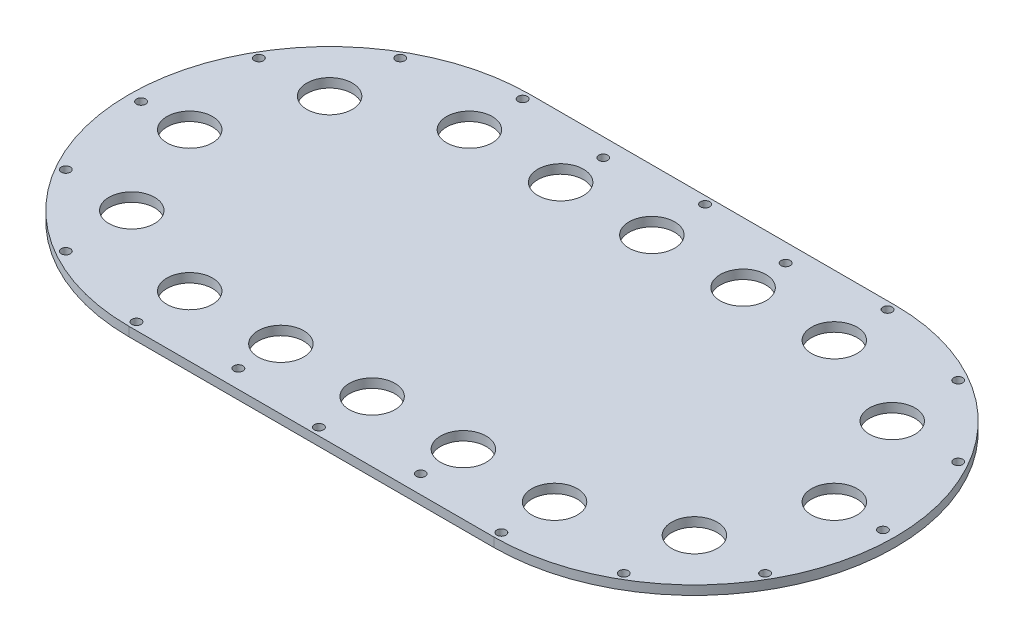
SolidWorks part; units mm, degrees
ref_plane "前视基准面" through (0, 0, 0) normal (0, 0, 1) x (1, 0, 0)
ref_plane "上视基准面" through (0, 0, 0) normal (0, 1, 0) x (1, 0, 0)
ref_plane "右视基准面" through (0, 0, 0) normal (1, 0, 0) x (0, 0, -1)
sketch "草图1" plane through (0, 0, 0) normal (0, 1, 0) x (1, 0, 0)
  line L0 (0, 0) -> (0, 89.0672) construction
  line L1 (-60, 0) -> (60, 0) construction
  line L2 (-60, 70) -> (60, 70)
  line L3 (-60, -70) -> (60, -70)
  line L4 (-90, 51.9615) -> (-60, 0) construction
  line L5 (-90, -51.9615) -> (-60, 0) construction
  line L8 (0, 0) -> (76.6344, 0) construction
  line L9 (-49.5811, 59.0885) -> (-60, 0) construction
  line L10 (-116.3816, -20.5212) -> (-60, 0) construction
  line L11 (-14.0373, -38.5673) -> (-60, 0) construction
  arc A2 (-60, 70) -> (-60, -70) centre (-60, 0) ccw
  arc A3 (60, -70) -> (60, 70) centre (60, 0) ccw
  circle A4 centre (0, 0) radius 1.5 construction
  circle A5 centre (-90, 51.9615) radius 1.5 construction
  circle A6 centre (-90, -51.9615) radius 1.5 construction
  circle A7 centre (90, -51.9615) radius 1.5 construction
  circle A8 centre (90, 51.9615) radius 1.5 construction
  circle A10 centre (-122, 0) radius 1.5
  circle A11 centre (122, 0) radius 1.5
  circle A12 centre (-30, 60) radius 1.5
  circle A13 centre (30, 60) radius 1.5
  circle A14 centre (30, -60) radius 1.5
  circle A15 centre (-30, -60) radius 1.5
  point P7 (0, 0)
  dimension "D4" = 3
  dimension "D7" = 3
  dimension "D9" = 3
  dimension "D10" = 60
  dimension "D12" = 3
  dimension "D13" = 62
  dimension "D14" = 62
  dimension "D15" = 3
  dimension "D16" = 3
  dimension "D18" = 60
  dimension "D8" = 120
  dimension "D11" = 120
  dimension "D17" = 30
  dimension "D20" = 60
  dimension "D21" = 80
  dimension "D24" = 120
  dimension "D26" = 60
  dimension "D27" = 120
extrude "凸台-拉伸2" add sketch "草图1" along normal blind 3
sketch "草图3" plane through (0, 3, 0) normal (0, 1, 0) x (1, 0, 0)
  line L2 (-60, -66) -> (60, -66)
  line L3 (60, 66) -> (-60, 66)
  line L4 (-60, -70) -> (60, -70)
  line L5 (60, 70) -> (-60, 70)
  line L6 (-60, -70) -> (60, -70)
  line L7 (60, 70) -> (-60, 70)
  arc A2 (60, -66) -> (60, 66) centre (60, 0) ccw
  arc A3 (-60, 66) -> (-60, -66) centre (-60, 0) ccw
  arc A4 (60, -70) -> (60, 70) centre (60, 0) ccw
  arc A5 (-60, 70) -> (-60, -70) centre (-60, 0) ccw
  arc A6 (60, -70) -> (60, 70) centre (60, 0) ccw
  arc A7 (-60, 70) -> (-60, -70) centre (-60, 0) ccw
  dimension "D1" = 0
  dimension "D2" = 4
extrude "切除-拉伸1" cut sketch "草图3" against normal blind 10
sketch "草图4" plane through (0, 3, 0) normal (0, 1, 0) x (1, 0, 0)
  line L0 (60, 46) -> (-60, 46) construction
  line L1 (-60, -46) -> (60, -46) construction
  line L2 (60, 66) -> (-60, 66)
  line L3 (-60, -66) -> (60, -66)
  line L4 (60, 66) -> (-60, 66) construction
  line L5 (-60, -66) -> (60, -66) construction
  line L6 (-92.5269, -32.5269) -> (-60, 0) construction
  line L7 (-60, 0) -> (-39.3991, 0) construction
  line L8 (0, 0) -> (-22.7346, 0) construction
  line L9 (0, 0) -> (0, 17.2758) construction
  arc A0 (-60, 46) -> (-60, -46) centre (-60, 0) ccw construction
  arc A1 (60, -46) -> (60, 46) centre (60, 0) ccw construction
  arc A2 (-60, 66) -> (-60, -66) centre (-60, 0) ccw
  arc A3 (60, -66) -> (60, 66) centre (60, 0) ccw
  arc A4 (-60, 66) -> (-60, -66) centre (-60, 0) ccw construction
  arc A5 (60, -66) -> (60, 66) centre (60, 0) ccw construction
  circle A6 centre (-106, 0) radius 7.5
  circle A7 centre (106, 0) radius 7.5
  circle A8 centre (0, 46) radius 7.5
  circle A9 centre (0, -46) radius 7.5
  circle A10 centre (-60, -46) radius 7.5
  circle A11 centre (60, -46) radius 7.5
  circle A12 centre (30, -46) radius 7.5
  circle A13 centre (-30, -46) radius 7.5
  circle A14 centre (-92.5269, -32.5269) radius 7.5
  circle A15 centre (60, 46) radius 7.5
  circle A16 centre (30, 46) radius 7.5
  circle A17 centre (-92.5269, 32.5269) radius 7.5
  circle A18 centre (-30, 46) radius 7.5
  circle A19 centre (-60, 46) radius 7.5
  circle A20 centre (92.5269, -32.5269) radius 7.5
  circle A21 centre (92.5269, 32.5269) radius 7.5
  dimension "D3" = 15
  dimension "D4" = 15
  dimension "D5" = 15
  dimension "D6" = 15
  dimension "D7" = 15
  dimension "D8" = 15
  dimension "D10" = 15
  dimension "D11" = 30
  dimension "D12" = 15
  dimension "D2" = 20
  dimension "D9" = 2
  dimension "D13" = 135
  dimension "D1" = 0
extrude "切除-拉伸2" cut sketch "草图4" against normal blind 10
sketch "草图5" plane through (0, 3, 0) normal (0, 1, 0) x (1, 0, 0)
  line L0 (60, 61) -> (32.2913, 61) construction
  line L1 (-60, -61) -> (-32.2913, -61) construction
  line L2 (60, 66) -> (-60, 66)
  line L3 (-60, -66) -> (60, -66)
  line L4 (60, 66) -> (-60, 66) construction
  line L5 (-60, -66) -> (60, -66) construction
  line L6 (-32.2913, 61) -> (-60, 61) construction
  line L7 (60, 61) -> (-60, 61) construction
  line L8 (27.7087, 61) -> (-27.7087, 61) construction
  line L9 (-27.7087, -61) -> (27.7087, -61) construction
  line L10 (-60, -61) -> (60, -61) construction
  line L11 (32.2913, -61) -> (60, -61) construction
  line L12 (0, 0) -> (30, 0) construction
  line L13 (0, 0) -> (0, 14.6541) construction
  line L14 (114.9926, 31.75) -> (60, 0) construction
  line L15 (91.75, 54.9926) -> (60, 0) construction
  line L16 (27.7087, -61) -> (-27.7087, -61) construction
  line L17 (-32.2913, -61) -> (-60, -61) construction
  line L18 (60, -66) -> (-60, -66) construction
  line L19 (60, -61) -> (32.2913, -61) construction
  arc A0 (-60, 61) -> (-120.9577, 2.2723) centre (-60, 0) ccw construction
  arc A1 (60, -61) -> (120.9577, -2.2723) centre (60, 0) ccw construction
  arc A2 (-60, 66) -> (-60, -66) centre (-60, 0) ccw
  arc A3 (60, -66) -> (60, 66) centre (60, 0) ccw
  arc A4 (-60, 66) -> (-60, -66) centre (-60, 0) ccw construction
  arc A5 (60, -66) -> (60, 66) centre (60, 0) ccw construction
  circle A6 centre (-60, 63.5) radius 1.5
  circle A7 centre (114.9926, 31.75) radius 1.5
  arc A8 (-27.7087, 61) -> (-32.2913, 61) centre (-30, 60) ccw construction
  arc A9 (32.2913, 61) -> (27.7087, 61) centre (30, 60) ccw construction
  arc A10 (-120.9577, 2.2723) -> (-120.9577, -2.2723) centre (-122, 0) ccw construction
  arc A11 (-120.9577, -2.2723) -> (-60, -61) centre (-60, 0) ccw construction
  arc A12 (-60, 61) -> (-60, -61) centre (-60, 0) ccw construction
  arc A13 (120.9577, -2.2723) -> (120.9577, 2.2723) centre (122, 0) ccw construction
  arc A14 (120.9577, 2.2723) -> (60, 61) centre (60, 0) ccw construction
  arc A15 (60, -61) -> (60, 61) centre (60, 0) ccw construction
  arc A16 (-32.2913, -61) -> (-27.7087, -61) centre (-30, -60) ccw construction
  arc A17 (27.7087, -61) -> (32.2913, -61) centre (30, -60) ccw construction
  circle A19 centre (0, 63.5) radius 1.5
  circle A21 centre (60, 63.5) radius 1.5
  circle A22 centre (-30, 63.5) radius 1.5 [skipped]
  circle A23 centre (30, 63.5) radius 1.5 [skipped]
  circle A24 centre (60, 0) radius 63.5 construction
  circle A25 centre (91.75, 54.9926) radius 1.5
  circle A26 centre (91.75, -54.9926) radius 1.5
  circle A27 centre (114.9926, -31.75) radius 1.5
  circle A28 centre (-91.75, -54.9926) radius 1.5
  circle A29 centre (-114.9926, -31.75) radius 1.5
  circle A30 centre (-91.75, 54.9926) radius 1.5
  circle A31 centre (-114.9926, 31.75) radius 1.5
  arc A32 (32.2913, -61) -> (27.7087, -61) centre (30, -60) cw construction
  arc A33 (-27.7087, -61) -> (-32.2913, -61) centre (-30, -60) cw construction
  circle A34 centre (60, -63.5) radius 1.5
  circle A35 centre (0, -63.5) radius 1.5
  circle A36 centre (-60, -63.5) radius 1.5
  dimension "D3" = 3
  dimension "D4" = 2.5
  dimension "D5" = 5
  dimension "D6" = 5
  dimension "D7" = 5
  dimension "D8" = 5
  dimension "D12" = 3
  dimension "D13" = 2.5
  dimension "D15" = 3
  dimension "D14" = 30
  dimension "D16" = 30
  dimension "D1" = 0
  dimension "D2" = 5
  dimension "D11" = 5
extrude "切除-拉伸3" cut sketch "草图5" against normal blind 10
